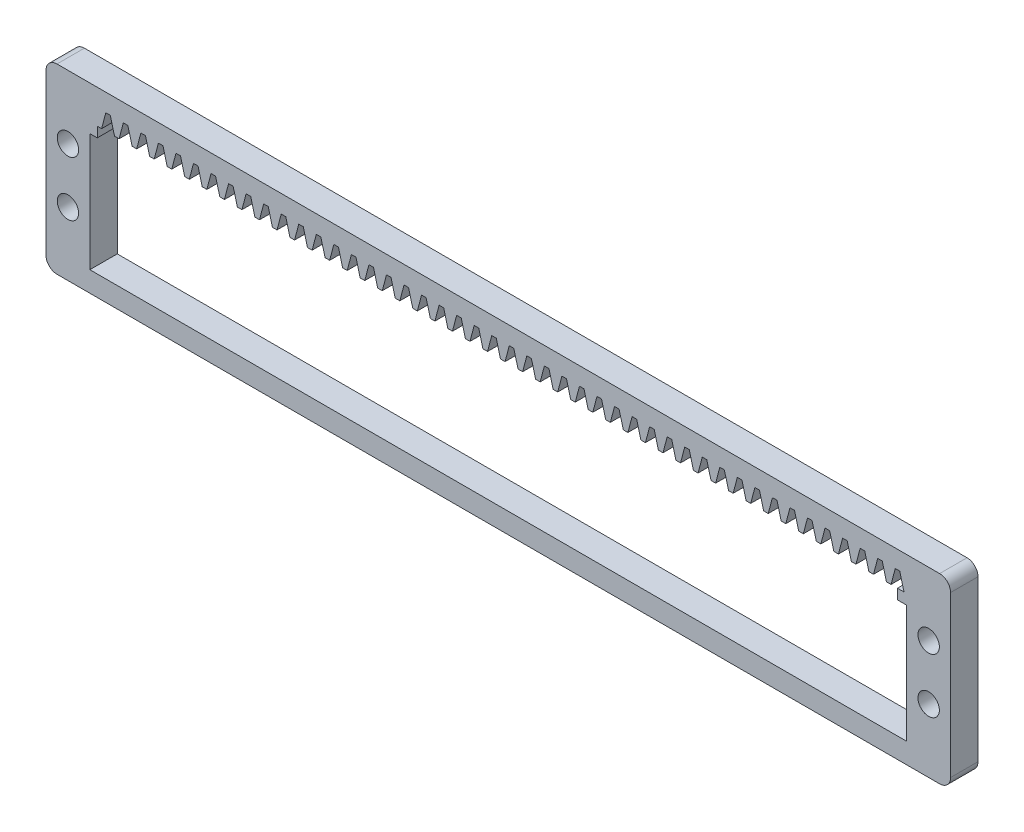
SolidWorks part; units mm, degrees
other "Markup1"
sketch "Sketch6" plane through (0, -30, 3.6) normal (0, 0, 1) x (1, 0, 0)
other "Markup2"
sketch "Sketch7" plane through (0, -30, 3.6) normal (0, 0, 1) x (1, 0, 0)
ref_plane "Front Plane" through (0, 0, 0) normal (0, 0, 1) x (1, 0, 0)
ref_plane "Top Plane" through (0, 0, 0) normal (0, 1, 0) x (1, 0, 0)
ref_plane "Right Plane" through (0, 0, 0) normal (1, 0, 0) x (0, 0, -1)
sketch "Sketch1" plane through (0, 0, 0) normal (0, 0, 1) x (1, 0, 0)
  line L1 (2, 0) -> (163, 0)
  line L2 (0, -2) -> (0, -31.22)
  line L3 (2, -33.22) -> (163, -33.22)
  line L4 (165, -2) -> (165, -31.22)
  arc A0 (163, -33.22) -> (165, -31.22) centre (163, -31.22) ccw
  arc A1 (0, -31.22) -> (2, -33.22) centre (2, -31.22) ccw
  arc A2 (2, 0) -> (0, -2) centre (2, -2) ccw
  arc A3 (163, 0) -> (165, -2) centre (163, -2) cw
  point P7 (165, -33.22)
  point P12 (0, 0)
  point P15 (165, 0)
  dimension "D3" = 2
  dimension "D1" = 33.22
  dimension "D2" = 165
extrude "Boss-Extrude1" add sketch "Sketch1" along normal blind 5
sketch "Sketch2" plane through (0, 0, 5) normal (0, 0, 1) x (1, 0, 0)
  line L0 (2, -33.22) -> (163, -33.22) construction
  line L1 (8, -8) -> (157, -8)
  line L2 (8, -8) -> (8, -29.5)
  line L3 (8, -29.5) -> (157, -29.5)
  line L4 (157, -8) -> (157, -29.5)
  line L5 (0, -2) -> (0, -31.22) construction
  line L7 (165, -31.22) -> (165, -2) construction
  line L8 (8, -18.75) -> (157, -18.75) construction
  line L12 (8, -29.5) -> (157, -29.5) construction
  line L13 (157, -4.3144) -> (157, -29.5) construction
  dimension "D1" = 21.5
  dimension "D2" = 8
  dimension "D3" = 8
  dimension "D4" = 3.72
extrude "Cut-Extrude1" cut sketch "Sketch2" against normal through all
sketch "Sketch3" plane through (0, 0, 5) normal (0, 0, 1) x (1, 0, 0)
  line L0 (157, -8) -> (8, -8) construction
  line L1 (9.35, -8) -> (155.32, -8)
  line L2 (9.35, -8) -> (9.35, -6.15)
  line L3 (9.35, -6.15) -> (155.32, -6.15)
  line L4 (155.32, -8) -> (155.32, -6.15)
  line L5 (157, -29.5) -> (157, -8) construction
  line L6 (8, -8) -> (8, -29.5) construction
  dimension "D1" = 1.85
  dimension "D2" = 1.68
  dimension "D3" = 1.35
extrude "Cut-Extrude2" cut sketch "Sketch3" against normal through all
sketch "Sketch4" plane through (0, 0, 5) normal (0, 0, 1) x (1, 0, 0)
  line L0 (157.7, -6.15) -> (156.5, -6.15) construction
  line L1 (155.32, -6.15) -> (9.35, -6.15) construction
  line L2 (157.7, -6.15) -> (158.465, -3.2492) construction
  line L3 (158.465, -3.2492) -> (155.735, -3.2492) construction
  line L4 (155.735, -3.2492) -> (156.5, -6.15)
  line L5 (155.735, -3.2492) -> (154.905, -3.2492)
  line L6 (154.905, -3.2492) -> (154.14, -6.15)
  line L7 (154.14, -6.15) -> (156.5, -6.15)
  line L10 (156.5, -6.15) -> (157.7, -6.15) construction
  dimension "D1" = 1.2
  dimension "D3" = 3
  dimension "D4" = 0.83
  dimension "D5" = 2.73
extrude "Cut-Extrude4" cut sketch "Sketch4" against normal through all
pattern_linear "LPattern1" count 46 spacing 3.2 along (-1, 0, 0) of "Cut-Extrude4"
sketch "Sketch5" plane through (0, 0, 5) normal (0, 0, 1) x (1, 0, 0)
  line L0 (157, -16.61) -> (165, -16.61) construction
  line L1 (163, 0) -> (2, 0) construction
  line L2 (8, -8) -> (8, -29.5) construction
  line L3 (0, -2) -> (0, -31.22) construction
  line L4 (2, -33.22) -> (163, -33.22) construction
  line L5 (0, -16.61) -> (8, -16.61) construction
  line L7 (161, -11.61) -> (161, -21.61) construction
  line L8 (4, -11.61) -> (4, -21.61) construction
  line L9 (157, -29.5) -> (157, -8) construction
  line L10 (165, -31.22) -> (165, -2) construction
  circle A4 centre (4, -11.61) radius 1.95
  circle A5 centre (4, -21.61) radius 1.95
  circle A6 centre (161, -11.61) radius 1.95
  circle A7 centre (161, -21.61) radius 1.95
  point P8 (161, -16.61)
  point P31 (161, -16.61)
  dimension "D1" = 3.9
  dimension "D2" = 4
  dimension "D3" = 3.9
  dimension "D4" = 3.9
  dimension "D6" = 3.9
  dimension "D5" = 10
  dimension "D7" = 10
extrude "Cut-Extrude5" cut sketch "Sketch5" against normal blind 10
